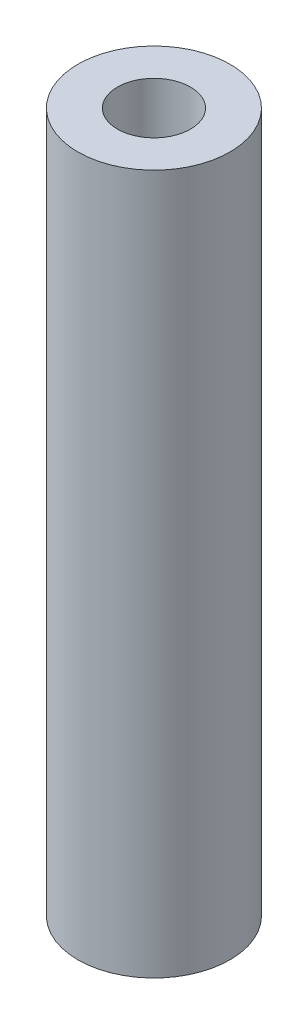
SolidWorks part; units mm, degrees
ref_plane "Front Plane" through (0, 0, 0) normal (0, 0, 1) x (1, 0, 0)
ref_plane "Top Plane" through (0, 0, 0) normal (0, 1, 0) x (1, 0, 0)
ref_plane "Right Plane" through (0, 0, 0) normal (1, 0, 0) x (0, 0, -1)
sketch "Sketch1" plane through (0, 0, 0) normal (0, 1, 0) x (1, 0, 0)
  circle A0 centre (0, 0) radius 1.2
  circle A1 centre (0, 0) radius 2.5
  dimension "D1" = 2.4
  dimension "D2" = 5
extrude "Boss-Extrude1" add sketch "Sketch1" along normal blind 23
